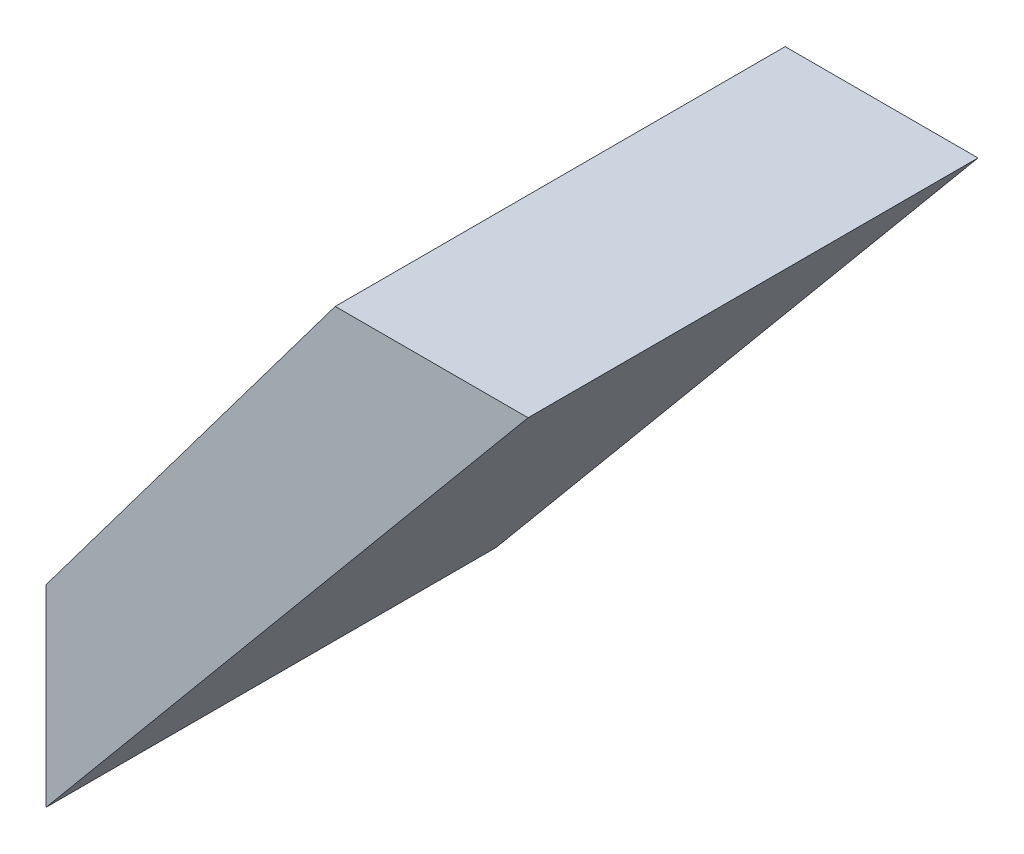
SolidWorks part; units mm, degrees
ref_plane "Front Plane" through (0, 0, 0) normal (0, 0, 1) x (1, 0, 0)
ref_plane "Top Plane" through (0, 0, 0) normal (0, 1, 0) x (1, 0, 0)
ref_plane "Right Plane" through (0, 0, 0) normal (1, 0, 0) x (0, 0, -1)
sketch "Sketch1" plane through (0, 0, 0) normal (0, 0, 1) x (1, 0, 0)
  line L0 (82.55, 0) -> (177.8, 114.3)
  line L1 (177.8, 114.3) -> (139.7, 114.3)
  line L2 (139.7, 114.3) -> (82.55, 38.1)
  line L3 (82.55, 38.1) -> (82.55, 0)
extrude "Boss-Extrude1" add sketch "Sketch1" against normal blind 88.9
